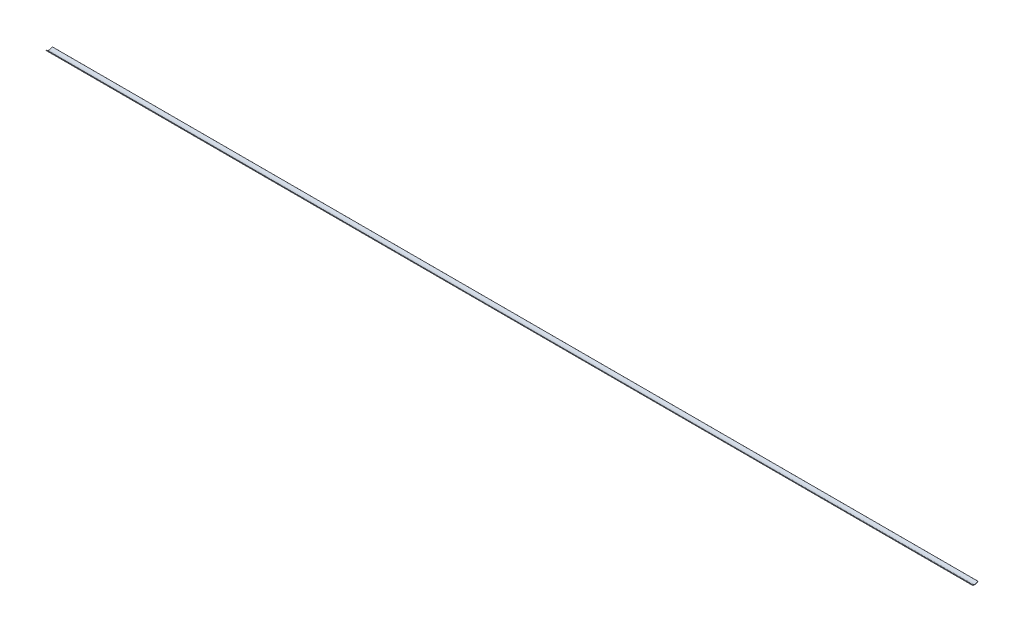
SolidWorks part; units mm, degrees
material "Plain Carbon Steel"
ref_plane "Front Plane" through (0, 0, 0) normal (0, 0, 1) x (1, 0, 0)
ref_plane "Top Plane" through (0, 0, 0) normal (0, 1, 0) x (1, 0, 0)
ref_plane "Right Plane" through (0, 0, 0) normal (1, 0, 0) x (0, 0, -1)
sketch "Sketch7" plane through (0, 0, 0) normal (1, 0, 0) x (0, 0, -1)
  line L0 (2.728, 26.9453) -> (2.4972, 27.1549)
  line L1 (-2.5578, 27.2235) -> (-2.7989, 27.0257)
  arc A1 (-2.7989, 27.0257) -> (2.728, 26.9453) centre (0, 29.4231) ccw
  arc A2 (2.4972, 27.1549) -> (-2.5578, 27.2235) centre (0, 29.4231) cw
extrude "Boss-Extrude7" add sketch "Sketch7" along normal blind 800
